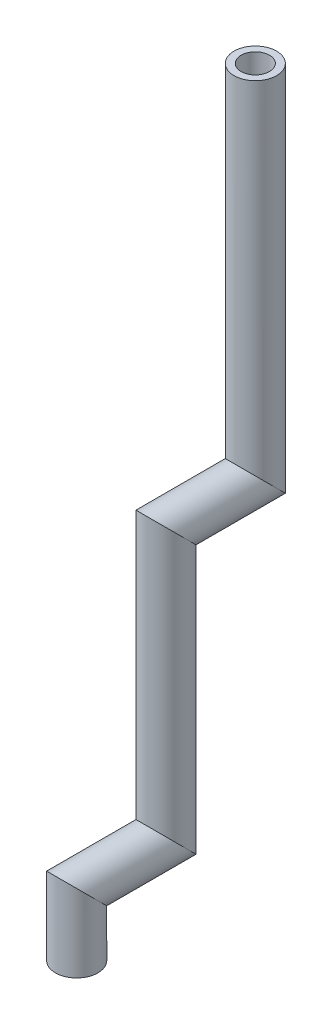
SolidWorks part; units mm, degrees
material "Silicon Rubber"
ref_plane "Front Plane" through (0, 0, 0) normal (0, 0, 1) x (1, 0, 0)
ref_plane "Top Plane" through (0, 0, 0) normal (0, 1, 0) x (1, 0, 0)
ref_plane "Right Plane" through (0, 0, 0) normal (1, 0, 0) x (0, 0, -1)
sketch "Sketch2" plane through (0, 0, 0) normal (0, 1, 0) x (1, 0, 0)
  line L0 (0, 2.5) -> (0, 8) construction
  line L1 (-17.5, 0) -> (17.5, 0) construction
  circle A0 centre (0, 0) radius 17.5 construction
  circle A1 centre (0, 0) radius 2.5 construction
  circle A2 centre (0, 8) radius 3.175
  circle A3 centre (0, 8) radius 4.7625
  circle A4 centre (0, -8) radius 3.175 construction
  circle A5 centre (0, -8) radius 4.7625 construction
  dimension "D1" = 35
  dimension "D2" = 5
  dimension "D4" = 6.35
  dimension "D5" = 9.525
  dimension "D3" = 5.5
sketch "Sketch4" plane through (0, 0, 0) normal (1, 0, 0) x (0, 0, -1)
  line L0 (8, 0) -> (8, 14)
  line L1 (8, 14) -> (28, 14)
  line L2 (28, 14) -> (28, 74)
  line L3 (28, 74) -> (48, 74)
  line L4 (48, 74) -> (48, 154)
  dimension "D1" = 14
  dimension "D2" = 20
  dimension "D3" = 60
  dimension "D4" = 20
  dimension "D5" = 80
sweep "Sweep2" add profiles "Sketch2" path "Sketch4"
ref_plane "Plane2" [suppressed] through (0, 158.9961, -275.3894) normal (0, 0.5, -0.866) x (1, 0, 0)
sketch "Sketch11" [suppressed] plane through (0, 158.9961, -275.3894) normal (0, 0.5, -0.866) x (1, 0, 0)
  line L0 (0, -123.4137) -> (0, -132.9387) construction
  line L1 (-4.7625, -128.1762) -> (4.7625, -128.1762) construction
  line L2 (0, -123.4137) -> (2, -123.4137) construction
  line L3 (0, -123.4137) -> (-2, -123.4137) construction
  line L4 (-2, -123.4137) -> (-2, -128.1762)
  line L5 (-2, -128.1762) -> (2, -128.1762)
  line L6 (2, -128.1762) -> (2, -123.4137)
  line L7 (2, -123.4137) -> (-2, -123.4137)
  circle A0 centre (0, -128.1762) radius 4.7625 construction
  dimension "D1" = 2
extrude "Cut-Extrude2" [suppressed] cut sketch "Sketch11" against normal blind 8
